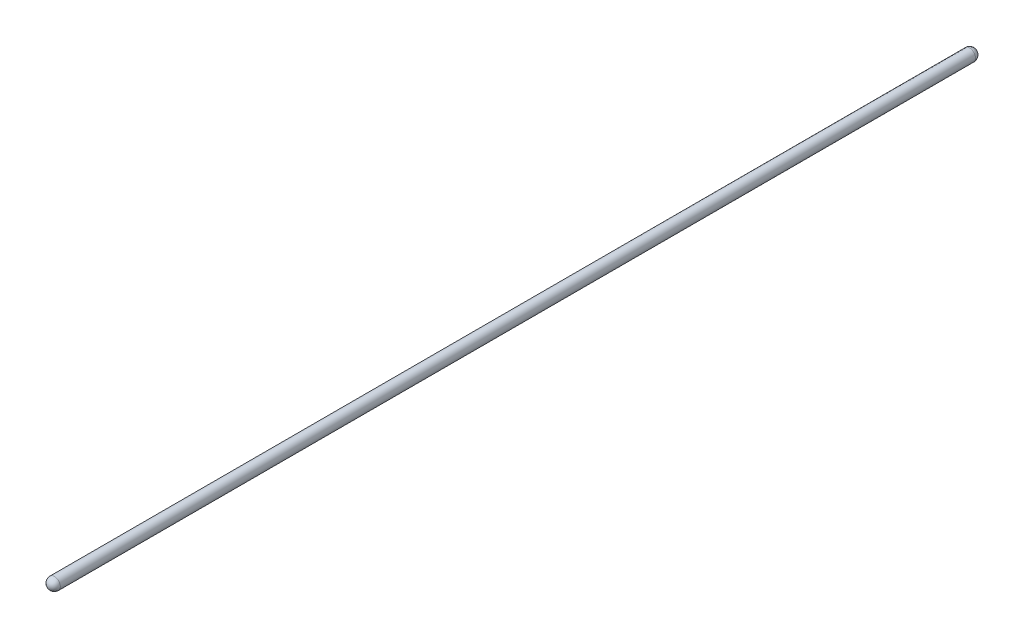
SolidWorks part; units mm, degrees
ref_plane "Front Plane" through (0, 0, 0) normal (0, 0, 1) x (1, 0, 0)
ref_plane "Top Plane" through (0, 0, 0) normal (0, 1, 0) x (1, 0, 0)
ref_plane "Right Plane" through (0, 0, 0) normal (1, 0, 0) x (0, 0, -1)
sketch "Sketch1" plane through (0, 0, 0) normal (0, 1, 0) x (1, 0, 0)
  line L0 (0, 0) -> (0, 9.525) construction
  line L1 (0, 0) -> (9.525, 0) construction
  line L2 (0, 0) -> (0, -1466.85) construction
  line L3 (0, -1466.85) -> (9.525, -1466.85) construction
  line L4 (0, -1466.85) -> (0, -1476.375) construction
  line L5 (9.525, 0) -> (9.525, -1466.85)
  line L6 (0, 9.525) -> (0, -1476.375)
  arc A1 (0, 9.525) -> (9.525, 0) centre (0, 0) cw
  arc A2 (9.525, -1466.85) -> (0, -1476.375) centre (0, -1466.85) cw
revolve "Revolve1" add sketch "Sketch1" angle 360 about L6
